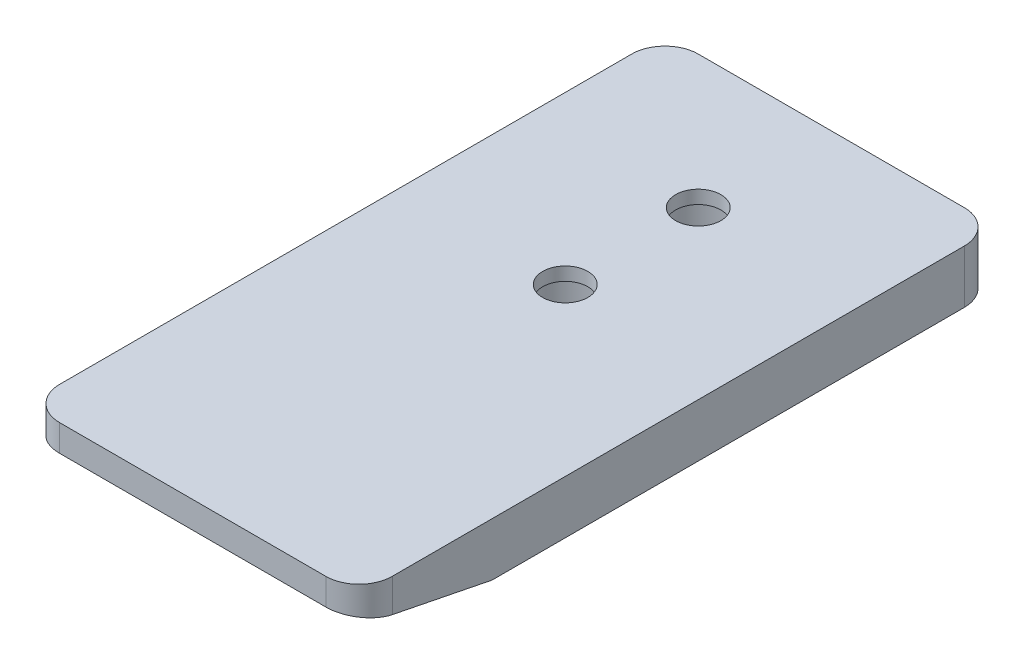
SolidWorks part; units mm, degrees
material "ABS"
ref_plane "Front Plane" through (0, 0, 0) normal (0, 0, 1) x (1, 0, 0)
ref_plane "Top Plane" through (0, 0, 0) normal (0, 1, 0) x (1, 0, 0)
ref_plane "Right Plane" through (0, 0, 0) normal (1, 0, 0) x (0, 0, -1)
sketch "Sketch1" plane through (0, 0, 0) normal (0, 1, 0) x (1, 0, 0)
  line L1 (0, 0) -> (25, 0)
  line L2 (0, 0) -> (0, 30)
  line L3 (0, 30) -> (25, 30)
  line L4 (25, 0) -> (25, 30)
  dimension "D1" = 30
  dimension "D2" = 25
extrude "Boss-Extrude1" add sketch "Sketch1" along normal blind 4
hole_wizard "CBORE for M3 SHCS2" positions "Sketch3" profile "Sketch4" counterbore size "M3" standard "ANSI Metric" end condition through all
sketch "Sketch3" plane through (0, 0, 0) normal (0, -1, 0) x (-1, 0, 0)
  line L0 (0, 30) -> (0, 0) construction
  line L1 (0, 0) -> (-25, 0) construction
  line L2 (-12.5, 10) -> (-12.5, 20)
  line L3 (-12.5, 15) -> (0, 15)
  point P0 (-12.5, 20)
  point P8 (-12.5, 0)
  point P31 (-12.5, 10)
  dimension "D1" = 10
sketch "Sketch4" plane through (12.5, 0, -20) normal (1, 0, 0) x (0, 0, -1)
  line L0 (0, 0) -> (0, 4)
  line L1 (0, 4) -> (1.7, 4)
  line L3 (1.7, 4) -> (1.7, 3)
  line L4 (1.7, 3) -> (3.25, 3)
  line L5 (3.25, 3) -> (3.25, 0)
  line L7 (3.25, 0) -> (0, 0)
  line L11 (0, -6.35) -> (0, 107.95) construction
  dimension "Thru Hole Dia." = 3.4
  dimension "Thru Hole Depth" = 4
  dimension "C'Bore Dia." = 6.5
  dimension "C'Bore Depth" = 3
sketch "Sketch5" plane through (0, 0, 0) normal (0, 0, 1) x (1, 0, 0)
  line L4 (0, 0) -> (25, 0)
  line L5 (25, 0) -> (25, 4)
  line L6 (25, 4) -> (0, 4)
  line L7 (0, 4) -> (0, 0)
  line L8 (0, 0) -> (25, 0)
  line L9 (25, 0) -> (25, 4)
  line L10 (25, 4) -> (0, 4)
  line L11 (0, 4) -> (0, 0)
  dimension "D1" = 0
extrude "Boss-Extrude2" add sketch "Sketch5" along normal blind 18
chamfer "Chamfer1" distance 10 distance2 2 1 edges at (12.5, 0, 18)
fillet "Fillet1" radius 2.5 4 edges at (0, 2, -30) (25, 2, -30) (0, 3, 18) (25, 3, 18)
